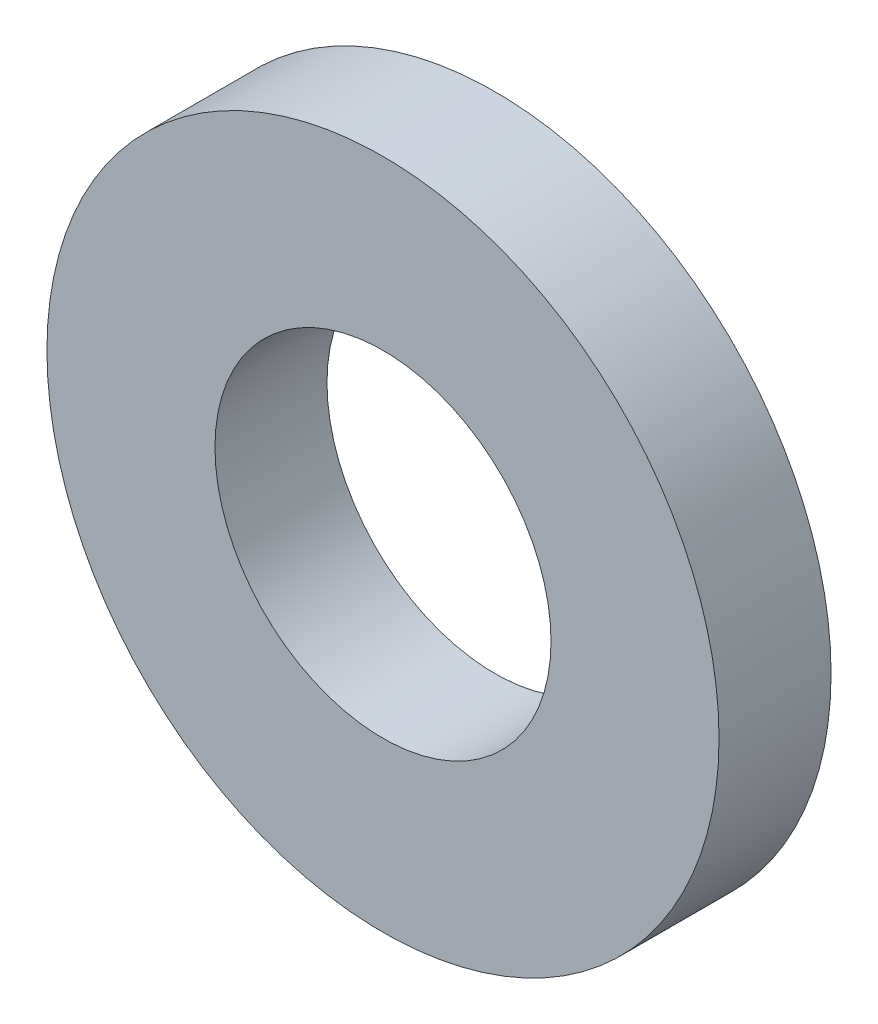
SolidWorks part; units mm, degrees
material "Nylon 6/10"
ref_plane "Front Plane" through (0, 0, 0) normal (0, 0, 1) x (1, 0, 0)
ref_plane "Top Plane" through (0, 0, 0) normal (0, 1, 0) x (1, 0, 0)
ref_plane "Right Plane" through (0, 0, 0) normal (1, 0, 0) x (0, 0, -1)
sketch "Sketch1" plane through (0, 0, 0) normal (0, 0, 1) x (1, 0, 0)
  circle A0 centre (0, 0) radius 3
  circle A1 centre (0, 0) radius 1.5
  dimension "D1" = 3
  dimension "D2" = 6
extrude "Boss-Extrude1" add sketch "Sketch1" along normal blind 1
